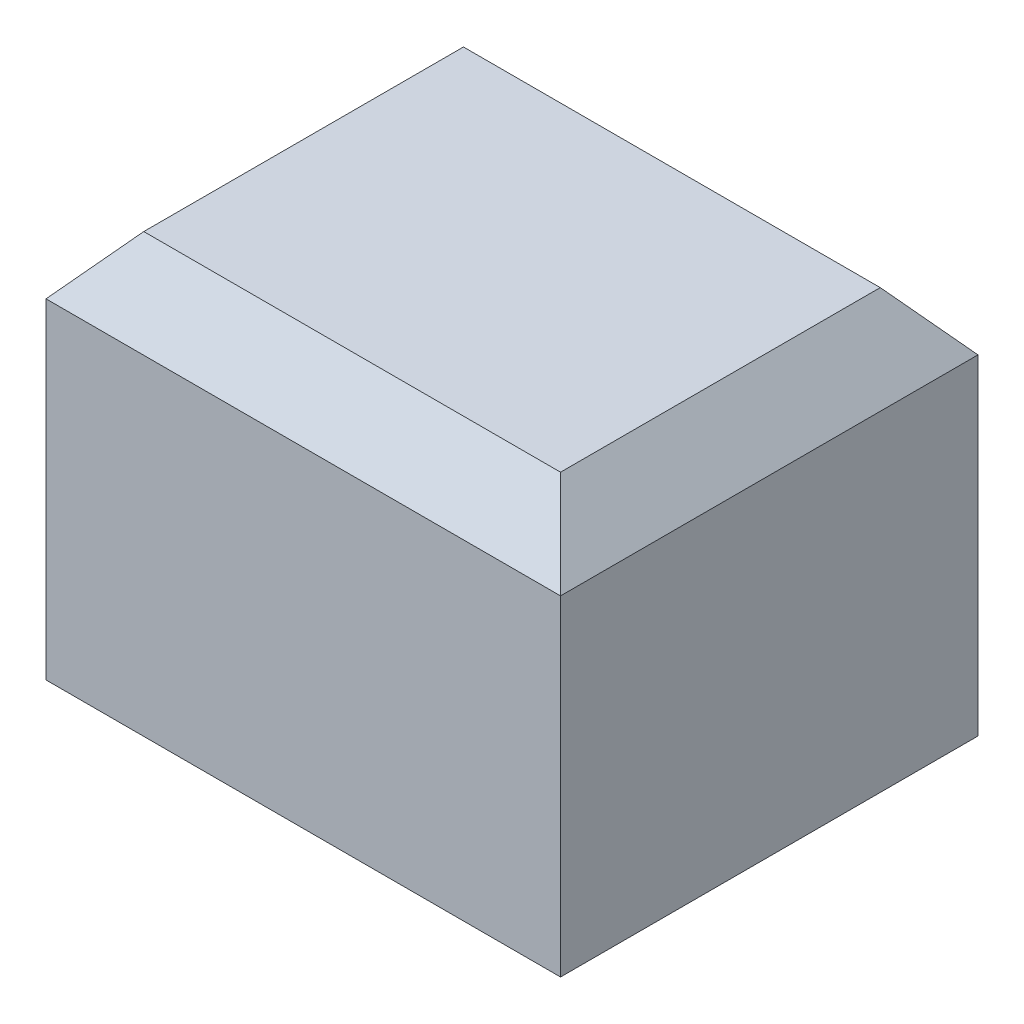
SolidWorks part; units mm, degrees
ref_plane "Front Plane" through (0, 0, 0) normal (0, 0, 1) x (1, 0, 0)
ref_plane "Top Plane" through (0, 0, 0) normal (0, 1, 0) x (1, 0, 0)
ref_plane "Right Plane" through (0, 0, 0) normal (1, 0, 0) x (0, 0, -1)
sketch "Sketch1" plane through (0, 0, 0) normal (0, 1, 0) x (1, 0, 0)
  line L0 (-2.65, -2.15) -> (2.65, -2.15)
  line L1 (-1.55, -1.05) -> (1.55, -1.05) construction
  line L2 (-1.55, -1.05) -> (-1.55, 1.05) construction
  line L3 (-1.55, 1.05) -> (1.55, 1.05) construction
  line L4 (1.55, -1.05) -> (1.55, 1.05) construction
  line L5 (-1.55, -1.05) -> (1.55, 1.05) construction
  line L6 (-1.55, 1.05) -> (1.55, -1.05) construction
  line L7 (2.65, -2.15) -> (2.65, 2.15)
  line L8 (-2.65, 2.15) -> (2.65, 2.15)
  line L9 (-2.65, -2.15) -> (-2.65, 2.15)
  line L15 (-1.55, -1.05) -> (1.55, -1.05)
  line L16 (-1.55, -1.05) -> (-1.55, 1.05)
  line L17 (-1.55, 1.05) -> (1.55, 1.05)
  line L18 (1.55, -1.05) -> (1.55, 1.05)
  point P0 (0, 0)
  dimension "D1" = 3.1
  dimension "D2" = 2.1
  dimension "D5" = 5.3
  dimension "D6" = 4.3
  dimension "D3" = 1.1
extrude "Body Extrude" add sketch "Sketch1" along normal blind 2.8
sketch "Sketch2" plane through (0, 2.8, 0) normal (0, 1, 0) x (1, 0, 0)
  line L1 (-2.65, -2.15) -> (2.65, -2.15)
  line L2 (-2.65, -2.15) -> (-2.65, 2.15)
  line L3 (-2.65, 2.15) -> (2.65, 2.15)
  line L4 (2.65, -2.15) -> (2.65, 2.15)
extrude "Cap Extrude" add sketch "Sketch2" along normal blind 1.2
chamfer "Bed Chamfer" distance 0.6 angle 40 4 edges at (0, 4, -2.15) (2.65, 4, 0) (0, 4, 2.15) (-2.65, 4, 0)
